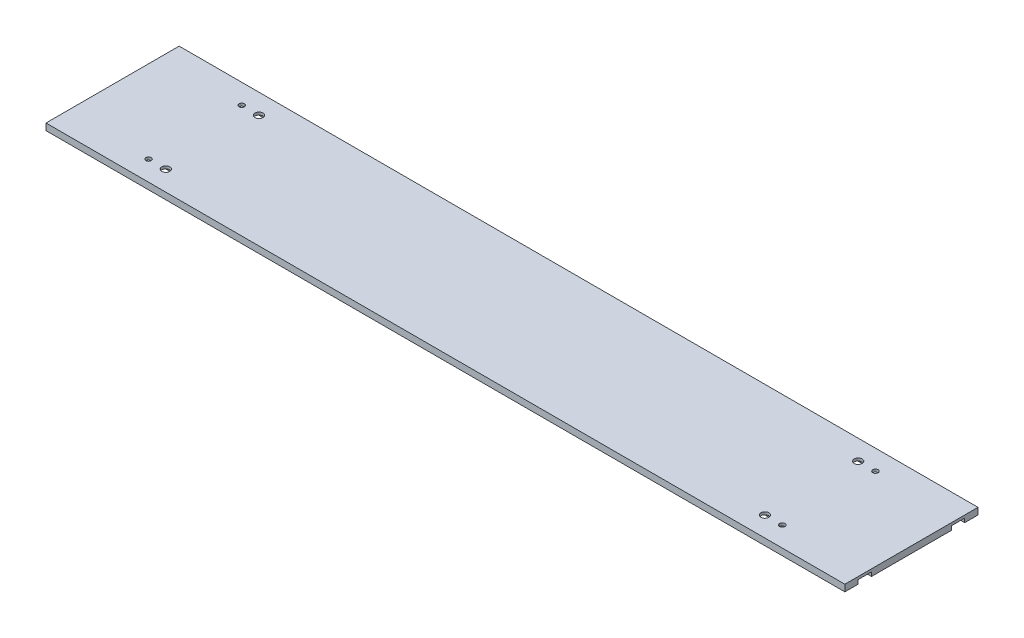
SolidWorks part; units mm, degrees
ref_plane "Front Plane" through (0, 0, 0) normal (0, 0, 1) x (1, 0, 0)
ref_plane "Top Plane" through (0, 0, 0) normal (0, 1, 0) x (1, 0, 0)
ref_plane "Right Plane" through (0, 0, 0) normal (1, 0, 0) x (0, 0, -1)
sketch "Sketch1" plane through (0, 0, 0) normal (0, 0, 1) x (1, 0, 0)
  line L0 (0, 0) -> (600, 0)
  line L1 (600, 0) -> (600, 5)
  line L2 (600, 5) -> (0, 5)
  line L3 (0, 5) -> (0, 0)
  dimension "D1" = 600
  dimension "D2" = 5
extrude "Boss-Extrude1" add sketch "Sketch1" against normal blind 100
sketch "Sketch6" plane through (0, 5, 0) normal (0, 1, 0) x (1, 0, 0)
  circle A0 centre (62, 85) radius 2
  circle A1 centre (62, 15) radius 2
  circle A2 centre (538, 85) radius 2
  circle A3 centre (538, 15) radius 2
extrude "Cut-Extrude2" cut sketch "Sketch6" against normal through all
sketch "Sketch7" plane through (0, 5, 0) normal (0, 1, 0) x (1, 0, 0)
  circle A0 centre (75, 85) radius 3
  circle A1 centre (75, 15) radius 3
  circle A2 centre (525, 85) radius 3
  circle A3 centre (525, 15) radius 3
extrude "Cut-Extrude3" cut sketch "Sketch7" against normal through all
sketch "Sketch8" plane through (0, 0, 0) normal (0, -1, 0) x (1, 0, 0)
  line L3 (0, -10) -> (600, -10)
  line L6 (600, -20) -> (0, -20)
  line L9 (0, -10) -> (0, -20)
  line L10 (600, -10) -> (600, -20)
  line L11 (600, -80) -> (600, -90)
  line L12 (0, -80) -> (0, -90)
  line L13 (0, -80) -> (600, -80)
  line L14 (0, -90) -> (600, -90)
extrude "Cut-Extrude5" cut sketch "Sketch8" against normal blind 3
